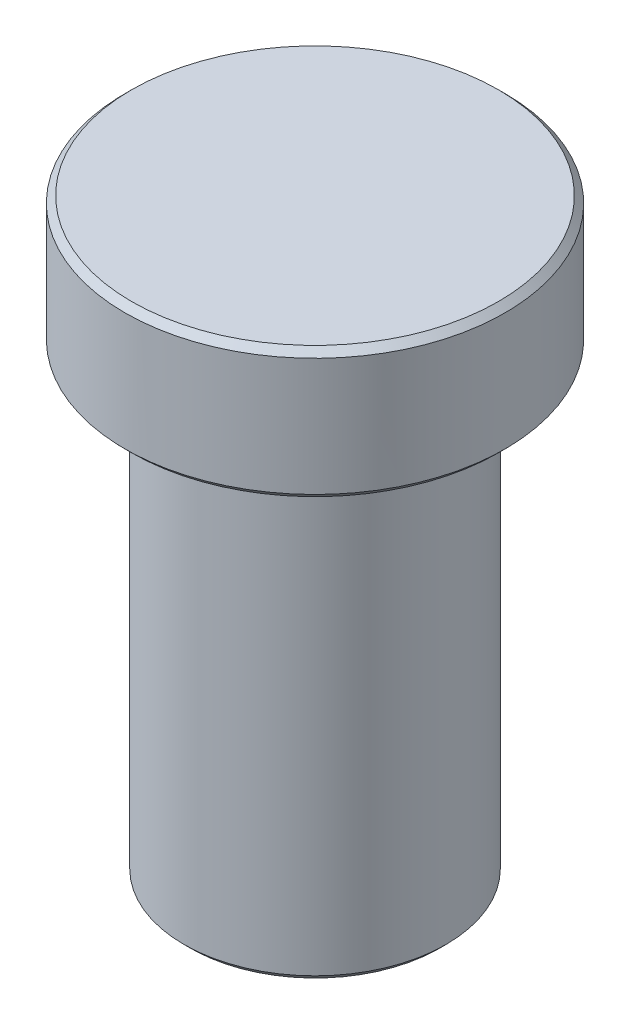
SolidWorks part; units mm, degrees
ref_plane "Front Plane" through (0, 0, 0) normal (0, 0, 1) x (1, 0, 0)
ref_plane "Top Plane" through (0, 0, 0) normal (0, 1, 0) x (1, 0, 0)
ref_plane "Right Plane" through (0, 0, 0) normal (1, 0, 0) x (0, 0, -1)
sketch "Sketch1" plane through (0, 0, 0) normal (0, 0, 1) x (1, 0, 0)
  line L0 (0, 0) -> (0, 9)
  line L1 (0, 9) -> (2.9, 9)
  line L2 (2.9, 9) -> (2.9, 7)
  line L3 (2.9, 7) -> (2, 7)
  line L4 (2, 7) -> (2, 0)
  line L5 (2, 0) -> (0, 0)
  dimension "D1" = 7
  dimension "D2" = 2.9
  dimension "D3" = 2
  dimension "D4" = 2
revolve "Revolve1" add sketch "Sketch1" angle 360 about L0
chamfer "Chamfer1" distance 0.1 angle 45 3 edges at (0, 7, -2.9) (0, 0, -2) (0, 9, -2.9)
